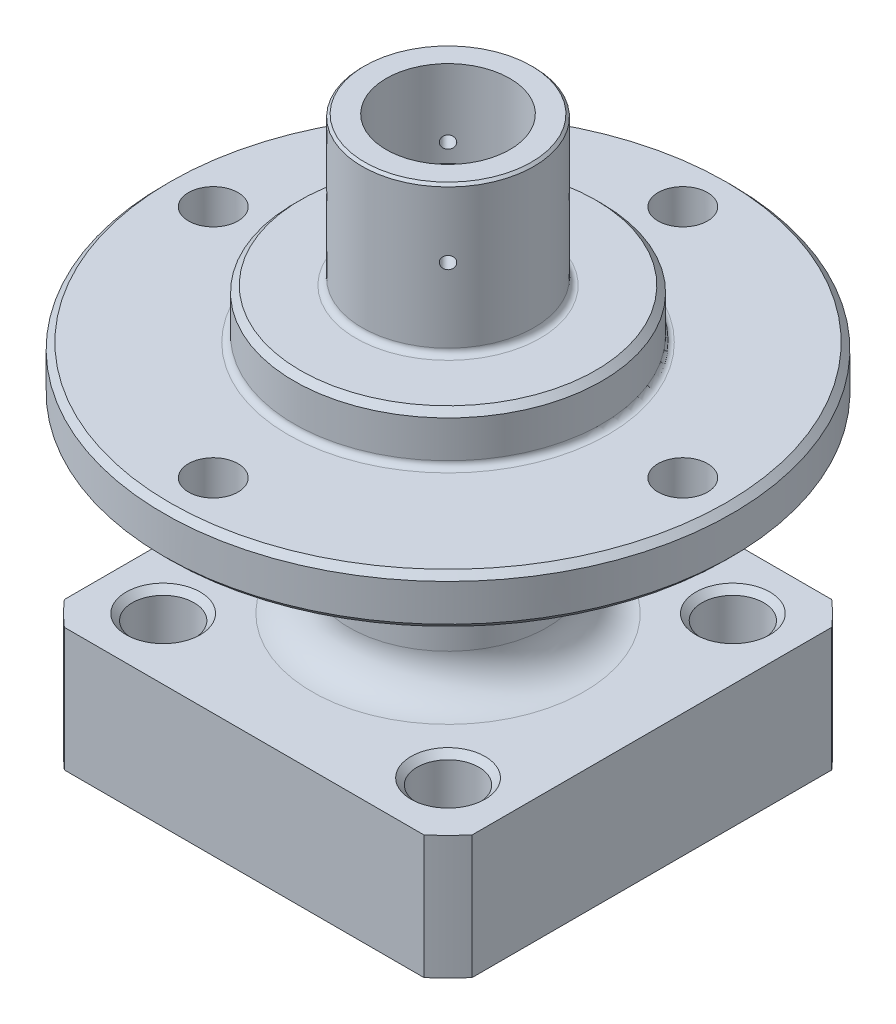
SolidWorks part; units mm, degrees
material "7075-T6 (SN)"
ref_plane "Front Plane" through (0, 0, 0) normal (0, 0, 1) x (1, 0, 0)
ref_plane "Top Plane" through (0, 0, 0) normal (0, 1, 0) x (1, 0, 0)
ref_plane "Right Plane" through (0, 0, 0) normal (1, 0, 0) x (0, 0, -1)
sketch "Sketch1" plane through (0, 0, 0) normal (0, 1, 0) x (1, 0, 0)
  line L0 (16.5, 16.5) -> (-16.5, -16.5) construction
  line L1 (-16.5, 16.5) -> (16.5, 16.5)
  line L2 (-16.5, 16.5) -> (-16.5, -16.5)
  line L3 (-16.5, -16.5) -> (16.5, -16.5)
  line L4 (16.5, 16.5) -> (16.5, -16.5)
  line L5 (-11.5258, 11.5258) -> (11.5258, 11.5258) construction
  line L6 (-11.5258, 11.5258) -> (-11.5258, -11.5258) construction
  line L7 (-11.5258, -11.5258) -> (11.5258, -11.5258) construction
  line L8 (11.5258, 11.5258) -> (11.5258, -11.5258) construction
  line L9 (-11.5258, 11.5258) -> (11.5258, -11.5258) construction
  line L11 (-43.2014, 36.4283) -> (48.0374, 36.4283)
  line L12 (-43.2014, 36.4283) -> (-43.2014, -38.3262)
  line L13 (-43.2014, -38.3262) -> (48.0374, -38.3262)
  line L14 (48.0374, 36.4283) -> (48.0374, -38.3262)
  circle A0 centre (0, 0) radius 4
  circle A1 centre (0, 0) radius 22
  circle A2 centre (-11.5258, 11.5258) radius 2.5
  circle A3 centre (11.5258, 11.5258) radius 2.5
  circle A4 centre (11.5258, -11.5258) radius 2.5
  circle A5 centre (-11.5258, -11.5258) radius 2.5
  dimension "D3" = 44
  dimension "D4" = 5
  dimension "D5" = 8
  dimension "D1" = 32.6
  dimension "D2" = 33
sketch "Sketch3" plane through (0, 0, 0) normal (0, 0, 1) x (1, 0, 0)
  line L0 (0, 0) -> (0, 43.0479) construction
  line L1 (-6.95, 45) -> (-5, 45)
  line L2 (-4, 0) -> (-22, 0)
  line L3 (-22, 0) -> (-22, 10)
  line L4 (-22, 10) -> (-8, 10)
  line L5 (-8, 10) -> (-8, 25)
  line L6 (-8, 25) -> (-23, 25)
  line L7 (-23, 25) -> (-23, 29)
  line L8 (-23, 29) -> (-12.45, 29)
  line L9 (-6.95, 33) -> (-6.95, 45)
  line L13 (-4, 25.6906) -> (-4, 0)
  line L14 (-5, 45) -> (-5, 38)
  line L15 (-5, 38) -> (0, 38)
  line L16 (0, 38) -> (0, 28)
  line L17 (-6.95, 33) -> (-12.45, 33)
  line L18 (-12.45, 33) -> (-12.45, 29)
  line L19 (0, 28) -> (-4, 25.6906)
  dimension "D1" = 10
  dimension "D2" = 13.9
  dimension "D3" = 10
  dimension "D4" = 7
  dimension "D5" = 4
  dimension "D6" = 46
  dimension "D7" = 15
  dimension "D8" = 16
  dimension "D9" = 16
  dimension "D10" = 24.9
  dimension "D11" = 4
  dimension "D12" = 10
  dimension "D13" = 60
revolve "Revolve1" add sketch "Sketch3" angle 360 about L0
extrude "Cut-Extrude1" cut sketch "Sketch1" along normal up to surface (10 mm away) contours L14 L11 L12 L13 A1 L4 L3 L2 L1 | L3 A1 | L2 A1 | L4 A1 | L1 A1 | A2 | A3 | A4 | A5
sketch "Sketch4" plane through (0, 29, 0) normal (0, 1, 0) x (1, 0, 0)
  line L1 (0, 0) -> (0, -19) construction
  circle A0 centre (0, -19) radius 2
  dimension "D1" = 4
  dimension "D2" = 19
extrude "Cut-Extrude2" cut sketch "Sketch4" against normal up to next (4 mm away)
pattern_circular "CirPattern1" count 4 over 360 about axis through (0, 0, 0) along (0, 1, 0) of "Cut-Extrude2"
sketch "Sketch5" plane through (0, 38, 0) normal (0, 1, 0) x (1, 0, 0)
  line L0 (0, 0) -> (2.1213, -2.1213) construction
  line L1 (0, 0) -> (0, -2.1021) construction
  circle A0 centre (2.1213, -2.1213) radius 0.7
  dimension "D1" = 1.4
  dimension "D2" = 3
  dimension "D3" = 45
extrude "Cut-Extrude3" cut sketch "Sketch5" against normal up to next
ref_plane "Plane1" through (4.9144, 0, -4.9144) normal (0.7071, 0, -0.7071) x (0, -1, 0)
sketch "Sketch6" plane through (4.9144, 0, -4.9144) normal (0.7071, 0, -0.7071) x (0, -1, 0)
  line L1 (-45, 6.95) -> (-45, -6.95) construction
  circle A0 centre (-39.5, 0) radius 0.5
  dimension "D1" = 1
  dimension "D2" = 5.5
extrude "Cut-Extrude4" cut sketch "Sketch6" against normal up to next
pattern_circular "CirPattern2" count 4 over 360 about axis through (0, 0, 0) along (0, 1, 0) of "Cut-Extrude3", "Cut-Extrude4"
sketch "Sketch8" plane through (-16.5, 0, 0) normal (-1, 0, 0) x (0, 0, 1)
  line L0 (-14.5516, 10) -> (14.5516, 0) construction
  circle A0 centre (0, 5) radius 2.5
  circle A1 centre (0, 5) radius 1
  dimension "D1" = 2
  dimension "D2" = 5
extrude "Cut-Extrude7" cut sketch "Sketch8" against normal up to next contours A1
hole_wizard "Ø5.0 (5) Diameter Hole1" positions "Sketch9" profile "Sketch10" hole size "Ø5.0" standard "ISO"
sketch "Sketch9" plane through (-16.5, 0, 0) normal (-1, 0, 0) x (0, 0, 1)
  point P0 (0, 5)
sketch "Sketch10" plane through (-16.5, 5, 0) normal (0, 1, 0) x (0, 0, 1)
  line L0 (0, 0) -> (0, 8)
  line L1 (0, 8) -> (2.5, 6.4978)
  line L2 (2.5, 6.4978) -> (2.5, 0)
  line L5 (2.5, 0) -> (0, 0)
  line L10 (0, 8) -> (-2.5, 6.4978) construction
  line L11 (0, -6.35) -> (0, 107.95) construction
  dimension "Hole Dia." = 5
  dimension "Hole Depth" = 8
  dimension "Drill Angle" = 118
cosmetic thread "Cosmetic Thread1" parameters "D2"=6
fillet "Fillet1" radius 0.5 2 edges at (0, 33, -6.95) (0, 29, -12.45)
chamfer "Chamfer1" distance 0.5 angle 45 12 edges at (0, 33, -12.45) (0, 25, -23) (0, 29, -23) (-11.5258, 0, 14.0258) (-11.5258, 10, 9.0258) (11.5258, 0, 14.0258) (11.5258, 10, 9.0258) (11.5258, 0, -9.0258) (11.5258, 10, -14.0258) (-11.5258, 0, -9.0258) (-11.5258, 10, -14.0258) (0, 0, -4)
fillet "Fillet2" radius 3 2 edges at (0, 25, -8) (0, 10, -8)
chamfer "Fase1" distance 0.2 angle 45 1 edges at (0, 45, -6.95)
